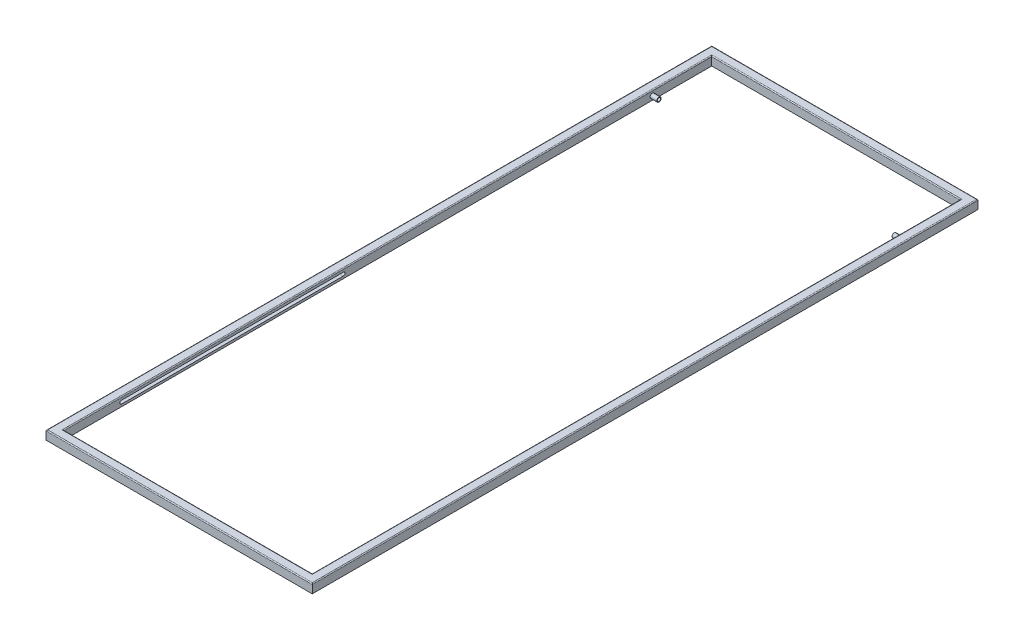
SolidWorks part; units mm, degrees
ref_plane "Alzado" through (0, 0, 0) normal (0, 0, 1) x (1, 0, 0)
ref_plane "Planta" through (0, 0, 0) normal (0, 1, 0) x (1, 0, 0)
ref_plane "Vista lateral" through (0, 0, 0) normal (1, 0, 0) x (0, 0, -1)
sketch "Croquis1" plane through (0, 0, 0) normal (0, 1, 0) x (1, 0, 0)
  line L0 (0, 750) -> (0, -750) construction
  line L1 (-300, -750) -> (300, -750)
  line L2 (-300, -750) -> (-300, 750)
  line L3 (-300, 750) -> (300, 750)
  line L4 (300, -750) -> (300, 750)
  line L5 (-300, -750) -> (300, 750) construction
  line L6 (-300, 750) -> (300, -750) construction
  line L7 (-280, -730) -> (280, -730)
  line L8 (-280, -730) -> (-280, 730)
  line L9 (-280, 730) -> (280, 730)
  line L10 (280, -730) -> (280, 730)
  line L11 (-280, -730) -> (280, 730) construction
  line L12 (-280, 730) -> (280, -730) construction
  line L13 (-300, 0) -> (300, 0) construction
  line L14 (-280, 730) -> (-300, 750) construction
  point P0 (0, 0)
  point P6 (0, 0)
  dimension "D1" = 600
  dimension "D2" = 1500
  dimension "D3" = 560
  dimension "D4" = 1460
extrude "Saliente-Extruir1" add sketch "Croquis1" along normal blind 20
sketch "Croquis2" plane through (0, 0, 0) normal (0, -1, 0) x (1, 0, 0)
  line L0 (-300, 750) -> (-280, 730) construction
  line L1 (0, 750) -> (0, -750) construction
  line L2 (-300, 750) -> (300, 750) construction
  line L3 (300, -750) -> (-300, -750) construction
  line L4 (-300, 0) -> (300, 0) construction
  line L5 (-300, -750) -> (-300, 750) construction
  line L6 (300, 750) -> (300, -750) construction
  circle A0 centre (-290, 740) radius 5
  circle A1 centre (290, 740) radius 5
  circle A2 centre (290, -740) radius 5
  circle A3 centre (-290, -740) radius 5
  dimension "D1" = 10
extrude "Cortar-Extruir1" cut sketch "Croquis2" against normal blind 15
fillet "Redondeo1" radius 2 8 edges at (0, 20, -730) (0, 20, -750) (280, 20, 0) (300, 20, 0) (0, 20, 730) (0, 20, 750) (-280, 20, 0) (-300, 20, 0)
sketch "Croquis4" plane through (280, 0, 0) normal (-1, 0, 0) x (0, 0, 1)
  line L0 (0, 18) -> (0, 0) construction
  line L1 (730, 18) -> (-730, 18) construction
  line L2 (730, 0) -> (-730, 0) construction
  line L3 (0, 12.75) -> (600, 12.75)
  line L4 (0, 5.25) -> (600, 5.25)
  line L5 (0, 9) -> (100, 9) construction
  line L6 (100, 9) -> (100, 12.75) construction
  line L7 (100, 12.75) -> (100, 5.25) construction
  line L8 (100, 5.25) -> (100, 12.75)
  arc A0 (600, 12.75) -> (600, 5.25) centre (600, 9) cw
  arc A1 (100, 12.75) -> (100, 5.25) centre (100, 9) ccw
  point P8 (0, 9)
  dimension "D1" = 3.75
  dimension "D2" = 600
  dimension "D3" = 3.75
  dimension "D4" = 600
  dimension "D5" = 100
extrude "Cortar-Extruir2" cut sketch "Croquis4" against normal blind 15 and the other way blind 575 contours A0 L3 L8 L4 | L8 A1
sketch "Croquis5" plane through (280, 0, 0) normal (-1, 0, 0) x (0, 0, 1)
  line L0 (0, 0) -> (0, 18) construction
  line L1 (730, 18) -> (-730, 18) construction
  line L2 (0, 9) -> (-596.25, 9) construction
  circle A0 centre (-596.25, 9) radius 5
  circle A1 centre (-596.25, 9) radius 3.75
  dimension "D2" = 10
  dimension "D3" = 7.5
  dimension "D1" = 596.25
extrude "Saliente-Extruir2" add sketch "Croquis5" along normal blind 15
mirror "Simetría1" about plane through (0, 0, 0) normal (1, 0, 0) of "Saliente-Extruir2"
scale "Escala1" scale about origin uniform scaling yes scale factor 1.3
